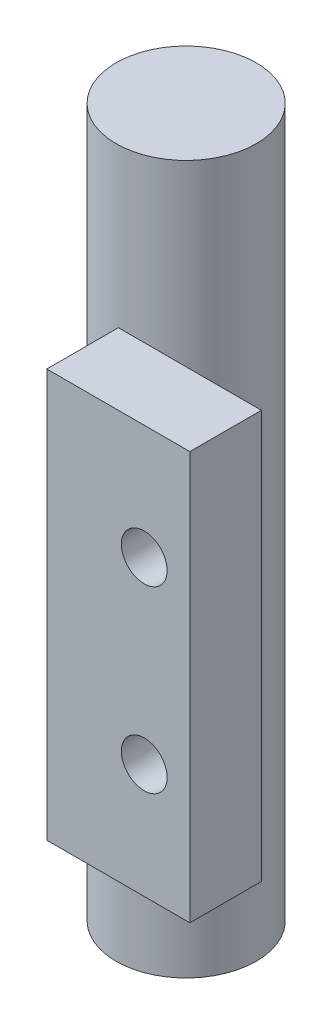
SolidWorks part; units mm, degrees
ref_plane "Front Plane" through (0, 0, 0) normal (0, 0, 1) x (1, 0, 0)
ref_plane "Top Plane" through (0, 0, 0) normal (0, 1, 0) x (1, 0, 0)
ref_plane "Right Plane" through (0, 0, 0) normal (1, 0, 0) x (0, 0, -1)
sketch "Sketch1" plane through (0, 0, 0) normal (0, 0, 1) x (1, 0, 0)
  line L0 (10, -1.47) -> (0, -1.47)
  line L1 (10, -1.47) -> (10, -30)
  line L2 (10, -30) -> (0, -30)
  line L3 (0, -1.47) -> (0, -30)
  dimension "D1" = 10
  dimension "D2" = 28.53
  dimension "D3" = 1.47
extrude "Boss-Extrude1" add sketch "Sketch1" along normal blind 5
sketch "Sketch2" plane through (0, 0, 0) normal (0, 0, -1) x (-1, 0, 0)
  line L0 (-10, -1.47) -> (0, -1.47) construction
  line L1 (-10, -30) -> (-10, -1.47) construction
  line L2 (0, -30) -> (-10, -30) construction
  circle A0 centre (-6.8103, -9.47) radius 1.6
  circle A1 centre (-6.8103, -22) radius 1.6
  dimension "D1" = 3.2
  dimension "D2" = 3.2
  dimension "D3" = 8
  dimension "D4" = 3.1897
  dimension "D5" = 8
  dimension "D6" = 3.1897
extrude "Cut-Extrude2" cut sketch "Sketch2" against normal blind 43
ref_plane "Plane1" through (0, 202.0162, 0) normal (0, 1, 0) x (0.8243, 0, 0.5661)
ref_plane "Plane2" through (0, -19.456, 0) normal (0, -1, 0) x (-1, 0, 0)
ref_plane "Plane3" through (0, -40.9652, 0) normal (0, -1, 0) x (-1, 0, 0)
sketch "Sketch10" plane through (0, -40.9652, 0) normal (0, -1, 0) x (1, 0, 0)
  circle A0 centre (-1.2141, -5.9555) radius 4.9
  dimension "D1" = 9.8
extrude "Boss-Extrude7" add sketch "Sketch10" against normal blind 49.5 separate body
